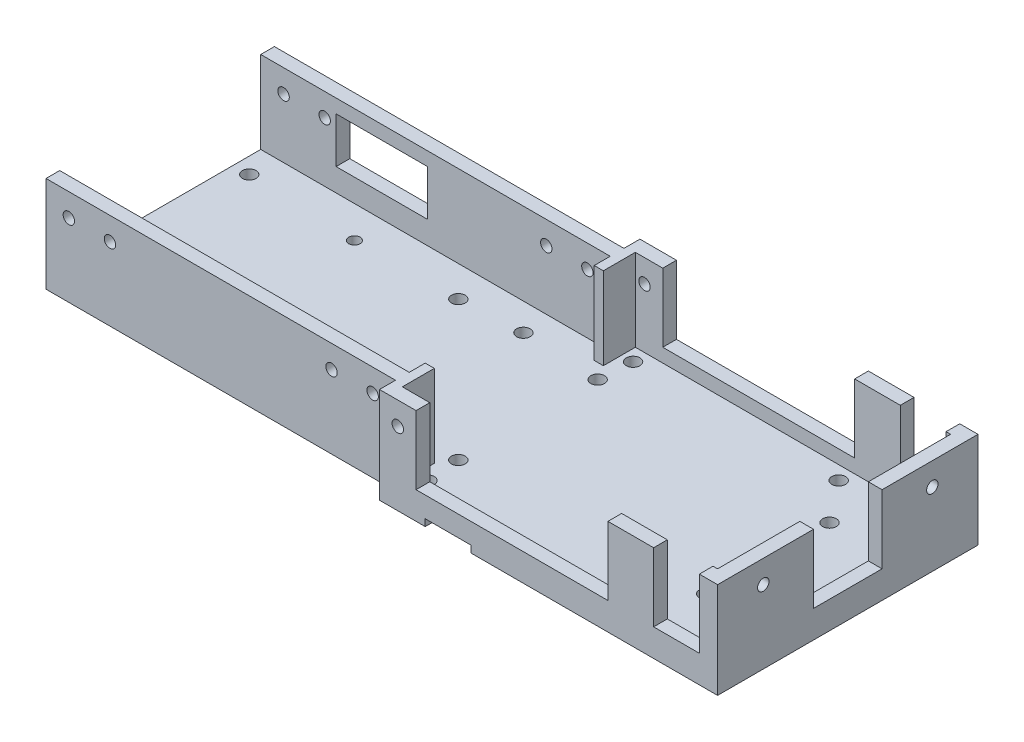
SolidWorks part; units mm, degrees
ref_plane "Front Plane" through (0, 0, 0) normal (0, 0, 1) x (1, 0, 0)
ref_plane "Top Plane" through (0, 0, 0) normal (0, 1, 0) x (1, 0, 0)
ref_plane "Right Plane" through (0, 0, 0) normal (1, 0, 0) x (0, 0, -1)
sketch "Sketch1" plane through (0, 0, 0) normal (0, 1, 0) x (1, 0, 0)
  line L1 (-115.1205, 21.9093) -> (35.3795, 21.9093)
  line L2 (-115.1205, 21.9093) -> (-115.1205, -28.0907)
  line L3 (-115.1205, -28.0907) -> (35.3795, -28.0907)
  line L4 (35.3795, 21.9093) -> (35.3795, -28.0907)
  dimension "D1" = 150.5
  dimension "D2" = 50
extrude "Boss-Extrude1" add sketch "Sketch1" along normal blind 3
sketch "Sketch2" plane through (0, 3, 0) normal (0, 1, 0) x (1, 0, 0)
  line L1 (35.3795, 21.9093) -> (-115.1205, 21.9093) construction
  line L2 (35.3795, -28.0907) -> (35.3795, 21.9093) construction
  line L3 (-115.1205, -28.0907) -> (35.3795, -28.0907) construction
  circle A0 centre (-65.1205, 12.1593) radius 1.5
  circle A1 centre (-65.1205, -18.3407) radius 1.5
  circle A2 centre (-34.6205, -18.3407) radius 1.5
  circle A3 centre (-34.6205, 12.1593) radius 1.5
  circle A6 centre (17.8795, -16.5907) radius 1.5
  circle A7 centre (17.8795, 10.4093) radius 1.5
  circle A8 centre (-111.6205, -19.0907) radius 1.5
  circle A9 centre (-111.6205, 12.9093) radius 1.5
  circle A13 centre (-87.6205, 11.9093) radius 1.25
  circle A14 centre (-87.6205, -18.0907) radius 1.25
  circle A15 centre (-51.6205, 12.9093) radius 1.5
  circle A16 centre (-51.6205, -19.0907) radius 1.5
  dimension "D1" = 3
  dimension "D2" = 3
  dimension "D3" = 3
  dimension "D4" = 3
  dimension "D13" = 17.5
  dimension "D14" = 17.5
  dimension "D19" = 3
  dimension "D20" = 3
  dimension "D25" = 3
  dimension "D26" = 3
  dimension "D37" = 2.5
  dimension "D38" = 2.5
  dimension "D43" = 3
  dimension "D44" = 3
  dimension "D5" = 52.5
  dimension "D6" = 9.75
  dimension "D7" = 52.5
  dimension "D8" = 30.5
  dimension "D9" = 30.5
  dimension "D10" = 30.5
  dimension "D11" = 9.75
  dimension "D12" = 30.5
  dimension "D15" = 17
  dimension "D16" = 17
  dimension "D17" = 22.5
  dimension "D18" = 22.5
  dimension "D23" = 27
  dimension "D24" = 11.5
  dimension "D27" = 32
  dimension "D28" = 9
  dimension "D39" = 30
  dimension "D42" = 10
  dimension "D45" = 60
  dimension "D46" = 60
  dimension "D47" = 32
  dimension "D48" = 9
extrude "Cut-Extrude1" cut sketch "Sketch2" against normal through all
sketch "Sketch4" plane through (0, 3, 0) normal (0, 1, 0) x (1, 0, 0)
  line L0 (35.3795, 21.9093) -> (-115.1205, 21.9093) construction
  line L1 (-38.6205, 25.4093) -> (35.3795, 25.4093)
  line L2 (-38.6205, 25.4093) -> (-38.6205, 21.9093)
  line L3 (-38.6205, 21.9093) -> (35.3795, 21.9093)
  line L4 (35.3795, 25.4093) -> (35.3795, 21.9093)
  line L5 (-38.6205, -28.0907) -> (35.3795, -28.0907)
  line L6 (-38.6205, -28.0907) -> (-38.6205, -31.5907)
  line L7 (-38.6205, -31.5907) -> (35.3795, -31.5907)
  line L8 (35.3795, -28.0907) -> (35.3795, -31.5907)
  line L9 (-115.1205, -28.0907) -> (35.3795, -28.0907) construction
  line L10 (35.3795, -28.0907) -> (35.3795, 21.9093) construction
  point P14 (35.3795, -29.8407)
  line M26 (-115.1205, -28.0907) -> (35.3795, -28.0907)
  dimension "D1" = 74
  dimension "D2" = 3.5
  dimension "D3" = 74
  dimension "D4" = 3.5
  dimension "D5" = 0
  dimension "D6" = 0
  dimension "D7" = 0
  dimension "D8" = 0
extrude "Boss-Extrude2" add sketch "Sketch4" against normal blind 3 contours L8 L6 L7 M26 | L2 L1 L4 L3
sketch "Sketch5" plane through (0, 3, 0) normal (0, 1, 0) x (1, 0, 0)
  line L0 (-38.6205, -31.5907) -> (35.3795, -31.5907) construction
  line L1 (-38.6205, 25.4093) -> (-38.6205, 21.9093) construction
  line L4 (-38.6205, -28.0907) -> (-38.6205, -31.5907) construction
  line L8 (-38.6205, 25.4093) -> (35.3795, 25.4093) construction
  circle A0 centre (-34.1205, 19.4093) radius 1.5
  circle A1 centre (-34.1205, -25.5907) radius 1.5
  circle A2 centre (10.8795, 19.4093) radius 1.5
  circle A3 centre (10.8795, -25.5907) radius 1.5
  circle A4 centre (-34.6205, 12.1593) radius 1.5 construction
  dimension "D1" = 3
  dimension "D2" = 3
  dimension "D3" = 3
  dimension "D4" = 3
  dimension "D5" = 45
  dimension "D6" = 45
  dimension "D7" = 45
  dimension "D8" = 45
  dimension "D9" = 6
  dimension "D10" = 4.5
  dimension "D11" = 4.5
  dimension "D12" = 6
extrude "Cut-Extrude3" cut sketch "Sketch5" against normal through all
sketch "Sketch6" plane through (0, 3, 0) normal (0, 1, 0) x (1, 0, 0)
  line L0 (31.3795, 25.4093) -> (35.3795, 25.4093)
  line L5 (31.3795, 25.4093) -> (31.3795, 22.4093)
  line L6 (31.3795, 22.4093) -> (35.3795, 22.4093)
  line L7 (35.3795, 25.4093) -> (35.3795, 22.4093)
  line L8 (31.3795, -28.5907) -> (35.3795, -28.5907)
  line L9 (31.3795, -28.5907) -> (31.3795, -31.5907)
  line L10 (31.3795, -31.5907) -> (35.3795, -31.5907)
  line L11 (35.3795, -28.5907) -> (35.3795, -31.5907)
  line L12 (32.3795, 22.4093) -> (35.3795, 22.4093)
  line L13 (32.3795, 22.4093) -> (32.3795, 4.4093)
  line L14 (32.3795, 4.4093) -> (35.3795, 4.4093)
  line L15 (35.3795, 22.4093) -> (35.3795, 4.4093)
  line L16 (32.3795, -10.5907) -> (35.3795, -10.5907)
  line L17 (32.3795, -10.5907) -> (32.3795, -28.5907)
  line L18 (32.3795, -28.5907) -> (35.3795, -28.5907)
  line L19 (35.3795, -10.5907) -> (35.3795, -28.5907)
  line L20 (35.3795, -31.5907) -> (35.3795, 25.4093) construction
  line L21 (-38.6205, 25.4093) -> (35.3795, 25.4093) construction
  line L22 (11.3795, 25.4093) -> (21.3795, 25.4093)
  line L23 (-38.6205, -31.5907) -> (35.3795, -31.5907) construction
  line L24 (-38.6205, 25.4093) -> (-30.6205, 25.4093)
  line L25 (-38.6205, 25.4093) -> (-38.6205, 22.4093)
  line L26 (-38.6205, 22.4093) -> (-30.6205, 22.4093)
  line L27 (-30.6205, 25.4093) -> (-30.6205, 22.4093)
  line L28 (-38.6205, 22.4093) -> (-36.6205, 22.4093)
  line L29 (-38.6205, 22.4093) -> (-38.6205, 15.4093)
  line L30 (-38.6205, 15.4093) -> (-36.6205, 15.4093)
  line L31 (-36.6205, 22.4093) -> (-36.6205, 15.4093)
  line L32 (-38.6205, -21.5907) -> (-36.6205, -21.5907)
  line L33 (-38.6205, -21.5907) -> (-38.6205, -28.5907)
  line L34 (-38.6205, -28.5907) -> (-36.6205, -28.5907)
  line L35 (-36.6205, -21.5907) -> (-36.6205, -28.5907)
  line L36 (-38.6205, -28.5907) -> (-30.6205, -28.5907)
  line L37 (-38.6205, -28.5907) -> (-38.6205, -31.5907)
  line L38 (-38.6205, -31.5907) -> (-30.6205, -31.5907)
  line L39 (-30.6205, -28.5907) -> (-30.6205, -31.5907)
  line L40 (-38.6205, 25.4093) -> (-38.6205, 21.9093) construction
  line L41 (-38.6205, -28.0907) -> (-38.6205, -31.5907) construction
  line L42 (11.3795, 25.4093) -> (11.3795, 22.4093)
  line L43 (11.3795, 22.4093) -> (21.3795, 22.4093)
  line L44 (-38.6205, 21.9093) -> (-115.1205, 21.9093) construction
  line L45 (-115.1205, 21.9093) -> (-38.6205, 21.9093)
  line L46 (-115.1205, 21.9093) -> (-115.1205, 18.9093)
  line L47 (-115.1205, 18.9093) -> (-38.6205, 18.9093)
  line L48 (-38.6205, 21.9093) -> (-38.6205, 18.9093)
  line L49 (-115.1205, -28.0907) -> (-38.6205, -28.0907) construction
  line L50 (-115.1205, -25.0907) -> (-38.6205, -25.0907)
  line L51 (-115.1205, -25.0907) -> (-115.1205, -28.0907)
  line L52 (-115.1205, -28.0907) -> (-38.6205, -28.0907)
  line L53 (-38.6205, -25.0907) -> (-38.6205, -28.0907)
  line L54 (21.3795, 25.4093) -> (21.3795, 22.4093)
  line L55 (11.3795, -28.5907) -> (21.3795, -28.5907)
  line L56 (11.3795, -28.5907) -> (11.3795, -31.5907)
  line L57 (11.3795, -31.5907) -> (21.3795, -31.5907)
  line L58 (21.3795, -28.5907) -> (21.3795, -31.5907)
  line L63 (-115.1205, 21.9093) -> (-115.1205, -28.0907) construction
  point P24 (35.3795, 23.9093)
  line M45 (35.3795, -31.5907) -> (35.3795, 25.4093)
  line M46 (35.3795, 25.4093) -> (-38.6205, 25.4093)
  dimension "D13" = 18
  dimension "D20" = 3
  dimension "D1" = 0
  dimension "D2" = 0
  dimension "D3" = 0
  dimension "D4" = 3
  dimension "D5" = 4
  dimension "D6" = 0
  dimension "D7" = 0
  dimension "D8" = 0
  dimension "D9" = 3
  dimension "D10" = 4
  dimension "D11" = 0
  dimension "D12" = 0
  dimension "D14" = 3
  dimension "D15" = 3
  dimension "D16" = 8
  dimension "D17" = 3
  dimension "D18" = 0
  dimension "D19" = 0
  dimension "D21" = 8
  dimension "D22" = 0
  dimension "D23" = 0
  dimension "D24" = 2
  dimension "D25" = 2
  dimension "D26" = 7
  dimension "D27" = 7
  dimension "D28" = 0
  dimension "D29" = 0
  dimension "D30" = 0
  dimension "D31" = 0
  dimension "D32" = 0
  dimension "D33" = 3
  dimension "D34" = 0
  dimension "D35" = 0
  dimension "D36" = 0
  dimension "D37" = 3
  dimension "D38" = 0
  dimension "D39" = 0
  dimension "D40" = 0
  dimension "D41" = 10
  dimension "D42" = 10
  dimension "D43" = 3
  dimension "D44" = 0
  dimension "D45" = 10
  dimension "D46" = 10
  dimension "D47" = 3
  dimension "D48" = 15
extrude "Boss-Extrude3" add sketch "Sketch6" along normal blind 18 contours L5 L6 M45 M46 | L50 L53 L52 L51 | L45 L48 L47 L46 | L24 L27 L26 L25 | L36 L39 L38 L37 | L33 L34 L35 L32 | L31 L30 L29 L28 | L11 L10 L9 L8 | L19 L18 L17 L16 | L15 L14 L13 L12 | L55 L58 L57 L56 | L22 L54 L43 L42
sketch "Sketch8" plane through (0, 3, 0) normal (0, 1, 0) x (1, 0, 0)
  line L0 (21.3795, -28.5907) -> (31.3795, -28.5907)
  line L5 (21.3795, -28.5907) -> (21.3795, -31.5907)
  line L6 (21.3795, -31.5907) -> (31.3795, -31.5907)
  line L7 (31.3795, -28.5907) -> (31.3795, -31.5907)
  line L8 (31.3795, -28.5907) -> (31.3795, -31.5907) construction
  line L9 (21.3795, -31.5907) -> (31.3795, -31.5907) construction
  line L11 (21.3795, -28.5907) -> (21.3795, -31.5907) construction
  line L12 (21.3795, 25.4093) -> (31.3795, 25.4093)
  line L13 (21.3795, 25.4093) -> (21.3795, 23.4093)
  line L14 (21.3795, 23.4093) -> (31.3795, 23.4093)
  line L15 (31.3795, 25.4093) -> (31.3795, 23.4093)
  line L16 (21.3795, 25.4093) -> (31.3795, 25.4093) construction
  line L17 (21.3795, 25.4093) -> (21.3795, 22.4093) construction
  line L18 (31.3795, 25.4093) -> (31.3795, 22.4093) construction
  line L19 (-30.6205, 25.4093) -> (11.3795, 25.4093)
  line L20 (-30.6205, 25.4093) -> (-30.6205, 22.4093)
  line L21 (-30.6205, 22.4093) -> (11.3795, 22.4093)
  line L22 (11.3795, 25.4093) -> (11.3795, 22.4093)
  line L23 (-30.6205, 25.4093) -> (11.3795, 25.4093) construction
  line L24 (11.3795, 25.4093) -> (11.3795, 22.4093) construction
  line L25 (-30.6205, 25.4093) -> (-30.6205, 22.4093) construction
  line L26 (-30.6205, -28.5907) -> (11.3795, -28.5907)
  line L27 (-30.6205, -28.5907) -> (-30.6205, -31.5907)
  line L28 (-30.6205, -31.5907) -> (11.3795, -31.5907)
  line L29 (11.3795, -28.5907) -> (11.3795, -31.5907)
  line L30 (-30.6205, -31.5907) -> (11.3795, -31.5907) construction
  line L31 (-30.6205, -28.5907) -> (-30.6205, -31.5907) construction
  line L32 (11.3795, -28.5907) -> (11.3795, -31.5907) construction
  line L33 (32.3795, 4.4093) -> (35.3795, 4.4093)
  line L34 (32.3795, 4.4093) -> (32.3795, -10.5907)
  line L35 (32.3795, -10.5907) -> (35.3795, -10.5907)
  line L36 (35.3795, 4.4093) -> (35.3795, -10.5907)
  line L38 (35.3795, -10.5907) -> (35.3795, 4.4093) construction
  line L39 (32.3795, 4.4093) -> (35.3795, 4.4093) construction
  line L40 (32.3795, -10.5907) -> (35.3795, -10.5907) construction
  dimension "D1" = 3
  dimension "D2" = 0
  dimension "D3" = 0
  dimension "D4" = 0
  dimension "D5" = 0
  dimension "D6" = 0
  dimension "D7" = 0
  dimension "D8" = 0
  dimension "D9" = 3
  dimension "D10" = 0
  dimension "D11" = 0
  dimension "D12" = 0
  dimension "D13" = 3
  dimension "D14" = 0
  dimension "D15" = 0
  dimension "D16" = 3
  dimension "D17" = 0
  dimension "D18" = 0
  dimension "D19" = 0
extrude "Boss-Extrude4" add sketch "Sketch8" along normal blind 3
sketch "Sketch9" plane through (0, 0, -21.9093) normal (0, 0, -1) x (-1, 0, 0)
  line L0 (38.6205, 0) -> (115.1205, 0) construction
  line L1 (98.6205, 8) -> (78.6205, 8)
  line L2 (98.6205, 8) -> (98.6205, 18)
  line L3 (98.6205, 18) -> (78.6205, 18)
  line L4 (78.6205, 8) -> (78.6205, 18)
  line L6 (38.6205, 0) -> (38.6205, 21) construction
  dimension "D1" = 20
  dimension "D2" = 10
  dimension "D3" = 8
  dimension "D4" = 40
extrude "Cut-Extrude4" cut sketch "Sketch9" against normal up to next
sketch "Sketch10" plane through (35.3795, 0, 0) normal (1, 0, 0) x (0, 0, -1)
  line L0 (-10.5907, 21) -> (-31.5907, 21) construction
  line L1 (-31.5907, 0) -> (-31.5907, 21) construction
  line L2 (25.4093, 0) -> (25.4093, 21) construction
  line L3 (25.4093, 21) -> (4.4093, 21) construction
  circle A0 centre (-21.5907, 16) radius 1.25
  circle A1 centre (15.4093, 16) radius 1.25
  dimension "D1" = 2.5
  dimension "D2" = 2.5
  dimension "D3" = 5
  dimension "D4" = 10
  dimension "D5" = 10
  dimension "D6" = 5
extrude "Cut-Extrude5" cut sketch "Sketch10" against normal up to next
sketch "Sketch11" plane through (0, 0, -21.9093) normal (0, 0, -1) x (-1, 0, 0)
  line L0 (115.1205, 21) -> (38.6205, 21) construction
  line L1 (38.6205, 0) -> (38.6205, 21) construction
  line L2 (115.1205, 21) -> (115.1205, 0) construction
  circle A0 centre (43.6205, 16) radius 1.25
  circle A1 centre (110.1205, 16) radius 1.25
  circle A2 centre (52.6205, 16) radius 1.25
  circle A3 centre (101.1205, 16) radius 1.25
  dimension "D1" = 2.5
  dimension "D2" = 2.5
  dimension "D7" = 2.5
  dimension "D10" = 2.5
  dimension "D3" = 5
  dimension "D4" = 5
  dimension "D5" = 5
  dimension "D6" = 5
  dimension "D8" = 5
  dimension "D9" = 14
  dimension "D11" = 14
  dimension "D12" = 5
extrude "Cut-Extrude6" cut sketch "Sketch11" against normal through all
sketch "Sketch12" plane through (0, 0, -25.4093) normal (0, 0, -1) x (-1, 0, 0)
  line L0 (38.6205, 21) -> (30.6205, 21) construction
  line L2 (38.6205, 0) -> (38.6205, 21) construction
  circle A0 centre (34.6205, 16) radius 1.25
  dimension "D1" = 2.5
  dimension "D2" = 5
  dimension "D3" = 4
extrude "Cut-Extrude7" cut sketch "Sketch12" against normal through all
sketch "Sketch13" plane through (0, 0, 0) normal (0, -1, 0) x (-1, 0, 0)
  line L0 (38.6205, -31.5907) -> (-35.3795, -31.5907) construction
  line L1 (28.6205, -31.5907) -> (18.6205, -31.5907)
  line L2 (28.6205, -31.5907) -> (28.6205, -30.0907)
  line L3 (28.6205, -30.0907) -> (18.6205, -30.0907)
  line L4 (18.6205, -31.5907) -> (18.6205, -30.0907)
  line L5 (28.6205, 25.4093) -> (18.6205, 25.4093)
  line L6 (28.6205, 25.4093) -> (28.6205, 23.9093)
  line L7 (28.6205, 23.9093) -> (18.6205, 23.9093)
  line L8 (18.6205, 25.4093) -> (18.6205, 23.9093)
  line L9 (38.6205, -28.0907) -> (38.6205, -31.5907) construction
  line L10 (38.6205, 25.4093) -> (-35.3795, 25.4093) construction
  line L11 (38.6205, 25.4093) -> (38.6205, 21.9093) construction
  point P14 (28.6205, 24.6593)
  dimension "D1" = 10
  dimension "D2" = 10
  dimension "D3" = 1.5
  dimension "D4" = 1.5
  dimension "D5" = 0
  dimension "D6" = 10
  dimension "D7" = 0
  dimension "D8" = 10
extrude "Cut-Extrude8" cut sketch "Sketch13" against normal blind 1.5
